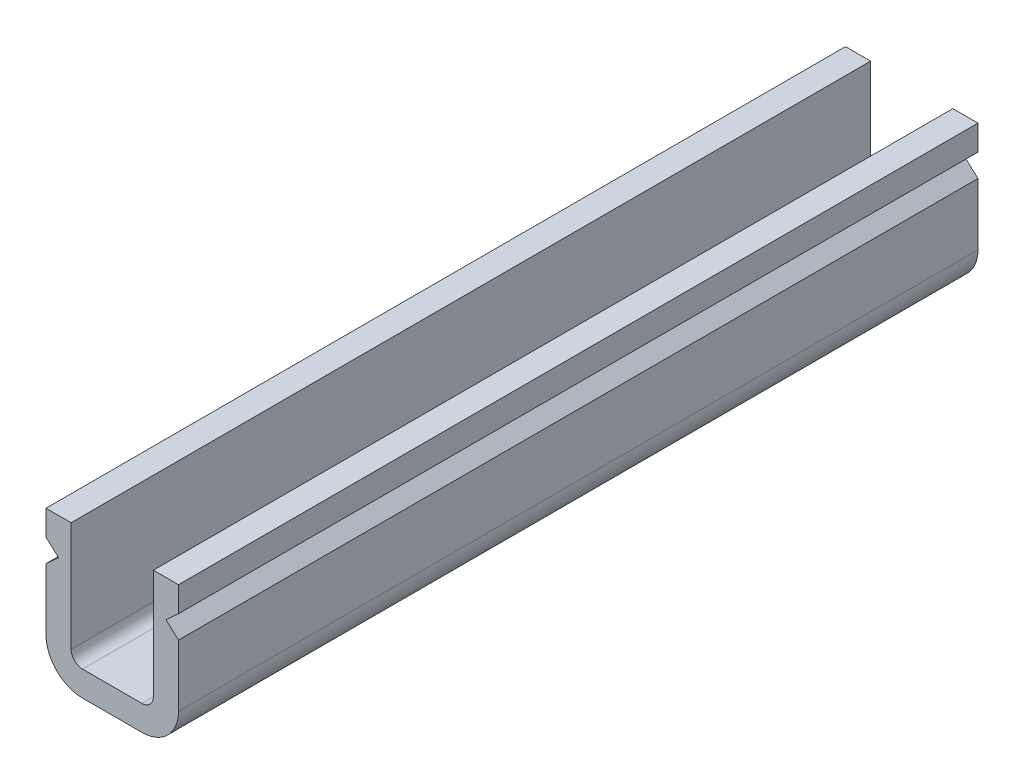
SolidWorks part; units mm, degrees
ref_plane "Plan de face" through (0, 0, 0) normal (0, 0, 1) x (1, 0, 0)
ref_plane "Plan de dessus" through (0, 0, 0) normal (0, 1, 0) x (1, 0, 0)
ref_plane "Plan de droite" through (0, 0, 0) normal (1, 0, 0) x (0, 0, -1)
sketch "Esquisse1" plane through (0, 0, 0) normal (0, 0, 1) x (1, 0, 0)
  line L0 (0, 0) -> (5.8, 0) construction
  line L1 (0, -1.1) -> (5.8, -1.1) construction
  line L2 (0.55, -1.6) -> (5.25, -1.6) construction
  line L3 (0, -2.1) -> (5.8, -2.1) construction
  line L4 (4.7, -4.8) -> (4.7, 0)
  line L22 (5.8, -1.1) -> (5.8, 0)
  line L23 (5.8, -2.1) -> (5.25, -1.6)
  line L24 (0, 0) -> (0, -1.1)
  line L25 (1.6, -6.4) -> (4.2, -6.4)
  line L26 (5.8, -4.8) -> (5.8, -2.1)
  line L27 (5.8, 0) -> (4.7, 0)
  line L28 (5.8, -1.1) -> (5.25, -1.6)
  line L29 (4.7, -5.3) -> (4.7, -2.5866) construction
  line L30 (1.1, -1.1) -> (1.1, -5.3) construction
  line L31 (1.1, 0) -> (0, 0)
  line L32 (5.8, 0) -> (0, 0) construction
  line L33 (1.1, 0) -> (1.1, -4.8)
  line L34 (1.6, -5.3) -> (4.2, -5.3)
  line L35 (4.7, -2.5866) -> (3.6147, -1.6) construction
  line L36 (4.1647, -1.1) -> (3.6147, -1.6) construction
  line L37 (4.1647, -1.1) -> (1.1, -1.1) construction
  line L38 (4.1647, -1.1) -> (4.1647, -1.1) construction
  line L39 (1.1, -5.3) -> (4.7, -5.3) construction
  line L40 (0, -1.1) -> (0.55, -1.6)
  line L41 (0, -2.1) -> (0.55, -1.6)
  line L42 (0, -2.1) -> (0, -4.8)
  line L43 (0, 0) -> (0, -6.4) construction
  line L44 (0, -6.4) -> (5.8, -6.4) construction
  line L45 (5.8, -6.4) -> (5.8, -2.1) construction
  arc A0 (1.1, -4.8) -> (1.6, -5.3) centre (1.6, -4.8) ccw
  arc A5 (4.7, -4.8) -> (4.2, -5.3) centre (4.2, -4.8) cw
  arc A6 (0, -4.8) -> (1.6, -6.4) centre (1.6, -4.8) ccw
  arc A7 (4.2, -6.4) -> (5.8, -4.8) centre (4.2, -4.8) ccw
  dimension "D2" = 0.5
  dimension "D3" = 1.1
  dimension "D4" = 1.6
  dimension "D9" = 0.5
  dimension "D1" = 1.1
  dimension "D5" = 2.7
  dimension "D6" = 4.8
  dimension "D7" = 2.6
  dimension "D8" = 0.55
  dimension "D10" = 0.55
extrude "Extrusion1" add sketch "Esquisse1" along normal blind 35
